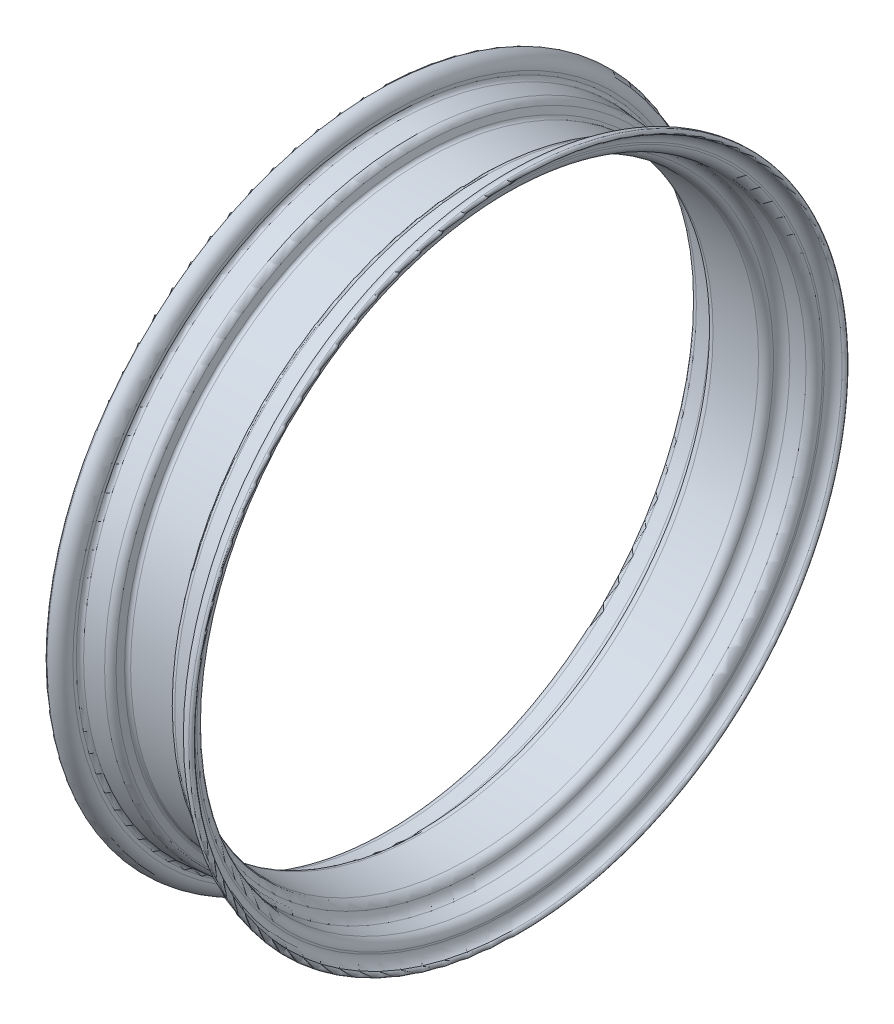
SolidWorks part; units mm, degrees
material "6061-T6 (SS)"
ref_plane "Front Plane" through (0, 0, 0) normal (0, 0, 1) x (1, 0, 0)
ref_plane "Top Plane" through (0, 0, 0) normal (0, 1, 0) x (1, 0, 0)
ref_plane "Right Plane" through (0, 0, 0) normal (1, 0, 0) x (0, 0, -1)
sketch "rimProfile" plane through (0, 0, 0) normal (0, 0, 1) x (1, 0, 0)
  line L0 (-85.5092, 0) -> (115.6652, 0) construction
  line L1 (0, 0) -> (0, 203) construction
  line L2 (0, 203) -> (-72.426, 203) construction
  line L3 (-35.7179, 202.9) -> (-23.0285, 201.7898)
  line L4 (-18.7658, 198.5189) -> (-17.2793, 194.4348)
  line L5 (-14.93, 192.7898) -> (14.93, 192.7898)
  line L6 (-38, 205.3905) -> (-38, 207.5883)
  line L7 (14.93, 192.7898) -> (14.93, 189.6148) construction
  line L8 (-46.5, 212.9133) -> (-46.5, 216.0883) construction
  line L9 (-14.93, 189.6148) -> (14.93, 189.6148)
  line L11 (-35.9754, 199.7433) -> (-26.1936, 198.8875)
  line L12 (-41.1665, 205.4084) -> (-41.1665, 206.6028)
  line L13 (46.5, 212.9133) -> (46.5, 216.0883) construction
  line L14 (41.1665, 205.4084) -> (41.1665, 206.6028)
  line L32 (35.9754, 199.7433) -> (26.1936, 198.8875)
  line L33 (-14.93, 192.7898) -> (-14.93, 189.6148) construction
  line L34 (38, 205.3905) -> (38, 207.5883)
  line L35 (18.7658, 198.5189) -> (17.2793, 194.4348)
  line L36 (35.7179, 202.9) -> (23.0285, 201.7898)
  arc A0 (-38, 207.5883) -> (-46.5, 216.0883) centre (-46.5, 207.5883) ccw
  arc A1 (-35.7179, 202.9) -> (-38, 205.3905) centre (-35.5, 205.3905) cw
  arc A2 (-17.2793, 194.4348) -> (-14.93, 192.7898) centre (-14.93, 195.2898) ccw
  arc A3 (-23.0285, 201.7898) -> (-18.7658, 198.5189) centre (-23.4642, 196.8088) cw
  arc A4 (-20.4442, 193.9485) -> (-14.93, 189.6148) centre (-14.93, 195.2898) ccw
  arc A6 (-35.9754, 199.7433) -> (-41.1665, 205.4084) centre (-35.4798, 205.4084) cw
  arc A22 (-20.4442, 193.9485) -> (-26.1936, 198.8875) centre (-26.7601, 192.4122) ccw
  arc A24 (-41.1665, 206.6028) -> (-46.5, 212.9133) centre (-47.5665, 206.6028) ccw
  arc A25 (-46.5, 216.0883) -> (-46.5, 212.9133) centre (-46.5, 214.5008) ccw
  arc A26 (46.5, 216.0883) -> (46.5, 212.9133) centre (46.5, 214.5008) cw
  arc A27 (41.1665, 206.6028) -> (46.5, 212.9133) centre (47.5665, 206.6028) cw
  arc A28 (20.4442, 193.9485) -> (26.1936, 198.8875) centre (26.7601, 192.4122) cw
  arc A29 (35.9754, 199.7433) -> (41.1665, 205.4084) centre (35.4798, 205.4084) ccw
  arc A30 (20.4442, 193.9485) -> (14.93, 189.6148) centre (14.93, 195.2898) cw
  arc A31 (23.0285, 201.7898) -> (18.7658, 198.5189) centre (23.4642, 196.8088) ccw
  arc A32 (17.2793, 194.4348) -> (14.93, 192.7898) centre (14.93, 195.2898) cw
  arc A33 (35.7179, 202.9) -> (38, 205.3905) centre (35.5, 205.3905) ccw
  arc A34 (38, 207.5883) -> (46.5, 216.0883) centre (46.5, 207.5883) cw
  point P6 (-48.0875, 214.5008)
  point P8 (0, 203)
  point P49 (0, 192.7898)
  point P58 (0, 189.6148)
  dimension "D5" = 2.5
  dimension "D7" = 8.5
  dimension "D9" = 2.5
  dimension "D10" = 5
  dimension "D19" = 94.5875
  dimension "D14" = 6.5
  dimension "D16" = 29.8601
  dimension "D18" = 6.4
  dimension "D21" = 3.1665
  dimension "D22" = 5.6867
  dimension "D3" = 202.9
  dimension "D4" = 20
  dimension "D6" = 175
  dimension "D8" = 9
  dimension "D11" = 76
  dimension "D12" = 14.93
  dimension "D13" = 2.1978
  dimension "D15" = 3.1671
  dimension "D17" = 3.175
  dimension "D24" = 1.1944
revolve "Revolve1" add sketch "rimProfile" angle 360 about L0
sketch "Sketch1" plane through (41.1665, 0, 0) normal (1, 0, 0) x (0, 0, -1)
  line L0 (-541.6501, -279.1942) -> (178.3499, -279.1942) construction
  line L1 (0, 0) -> (96.1753, -193.5057)
  line L2 (37.4398, -57.9591) -> (96.1753, -182.8524)
  circle A0 centre (0, 0) radius 47
  circle A1 centre (0, 0) radius 58 construction
  circle A2 centre (0, 0) radius 69
  circle A3 centre (0, 0) radius 216.0883 construction
  circle A4 centre (0, 0) radius 206.6028 construction
  dimension "D1" = 94
  dimension "D2" = 116
  dimension "D3" = 11
  dimension "D4" = 11
